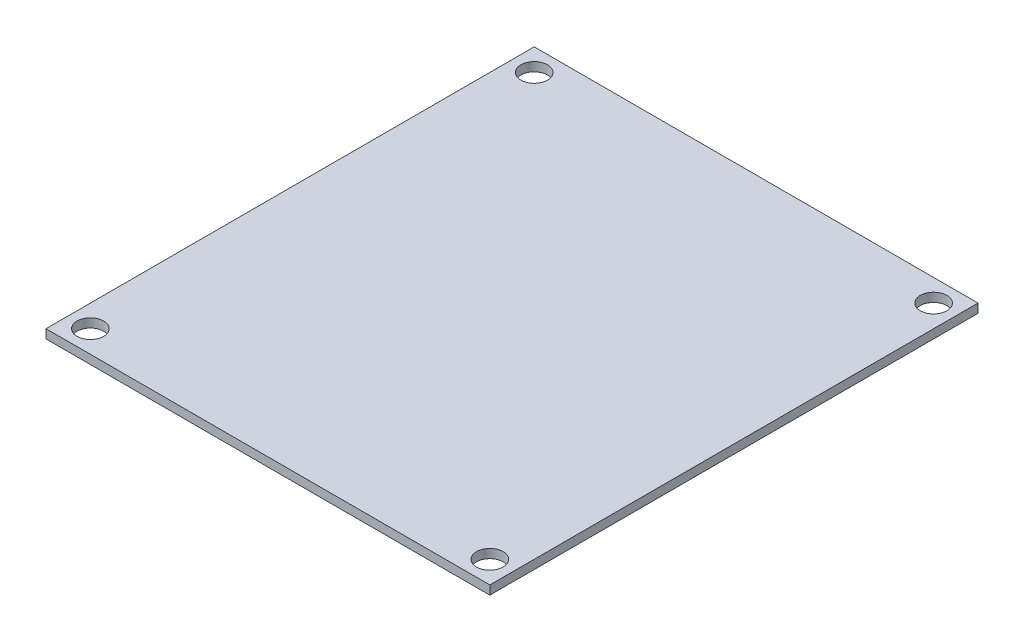
SolidWorks part; units mm, degrees
ref_plane "Front Plane" through (0, 0, 0) normal (0, 0, 1) x (1, 0, 0)
ref_plane "Top Plane" through (0, 0, 0) normal (0, 1, 0) x (1, 0, 0)
ref_plane "Right Plane" through (0, 0, 0) normal (1, 0, 0) x (0, 0, -1)
sketch "Sketch1" plane through (0, 0, 0) normal (0, 1, 0) x (1, 0, 0)
  line L1 (0, 0) -> (50, 0)
  line L2 (0, 0) -> (0, -55)
  line L3 (0, -55) -> (50, -55)
  line L4 (50, 0) -> (50, -55)
  dimension "D1" = 50
  dimension "D2" = 55
extrude "Boss-Extrude1" add sketch "Sketch1" along normal blind 1
sketch "Sketch2" plane through (0, 1, 0) normal (0, 1, 0) x (1, 0, 0)
  line L0 (0, 0) -> (0, -55) construction
  line L1 (50, 0) -> (0, 0) construction
  line L2 (25, 0) -> (25, -55) construction
  line L3 (0, -55) -> (50, -55) construction
  line L4 (0, -27.5) -> (50, -27.5) construction
  line L5 (50, -55) -> (50, 0) construction
  circle A0 centre (2.5, -2.5) radius 1.5
  circle A1 centre (47.5, -2.5) radius 1.5
  circle A2 centre (47.5, -52.5) radius 1.5
  circle A3 centre (2.5, -52.5) radius 1.5
  dimension "D1" = 3
  dimension "D2" = 2.5
  dimension "D3" = 2.5
extrude "Cut-Extrude1" cut sketch "Sketch2" against normal through all
